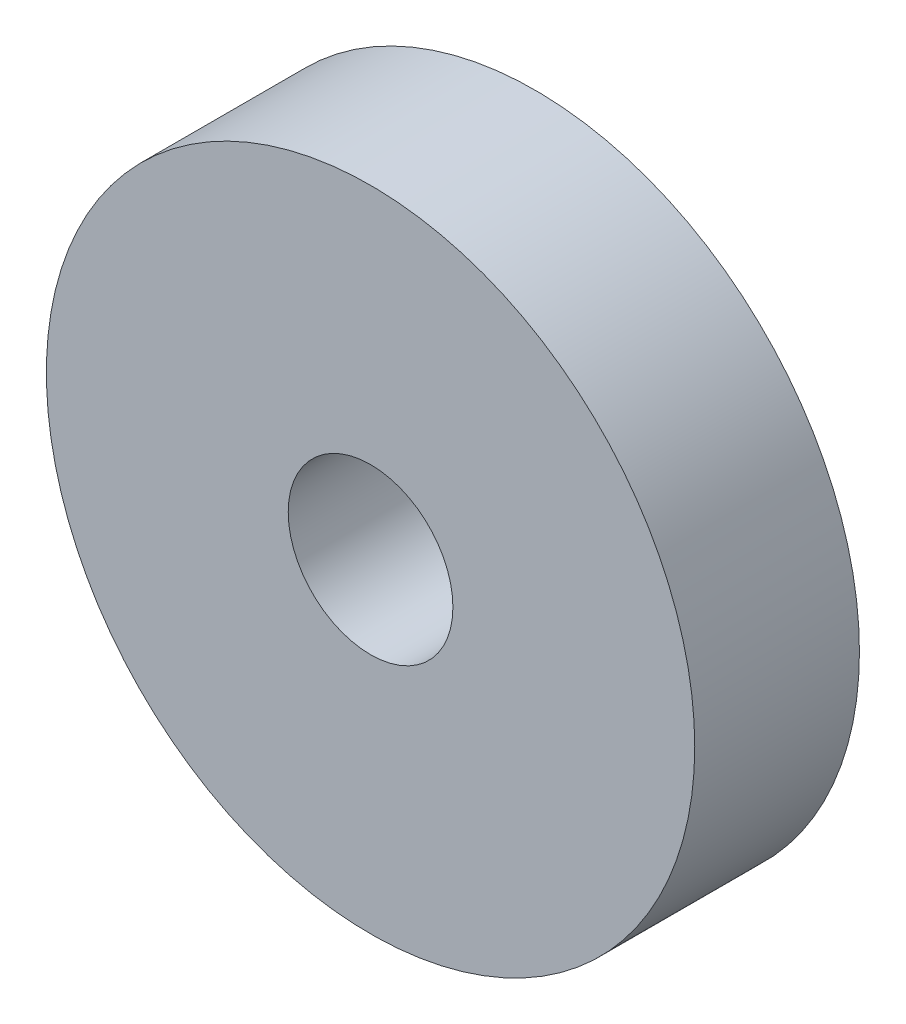
SolidWorks part; units mm, degrees
material "Balsa"
ref_plane "Front Plane" through (0, 0, 0) normal (0, 0, 1) x (1, 0, 0)
ref_plane "Top Plane" through (0, 0, 0) normal (0, 1, 0) x (1, 0, 0)
ref_plane "Right Plane" through (0, 0, 0) normal (1, 0, 0) x (0, 0, -1)
sketch "Sketch1" plane through (0, 0, 0) normal (0, 0, 1) x (1, 0, 0)
  circle A0 centre (0, 0) radius 12.5
  dimension "D1" = 25
extrude "Boss-Extrude1" add sketch "Sketch1" along normal blind 6.35
hole_wizard "1/4 (0.25) Diameter Hole1" positions "Sketch3" profile "Sketch2" hole size "1/4" standard "Ansi Inch"
sketch "Sketch3" plane through (0, 0, 0) normal (0, 0, -1) x (-1, 0, 0)
  point P1 (0, 0)
sketch "Sketch2" plane through (0, 0, 0) normal (1, 0, 0) x (0, 1, 0)
  line L0 (0, 0) -> (0, 19.9077)
  line L1 (0, 19.9077) -> (3.175, 18)
  line L2 (3.175, 18) -> (3.175, 0)
  line L5 (3.175, 0) -> (0, 0)
  line L10 (0, 19.9077) -> (-3.175, 18) construction
  line L11 (0, -6.35) -> (0, 107.95) construction
  dimension "Hole Dia." = 6.35
  dimension "Hole Depth" = 18
  dimension "Drill Angle" = 118
